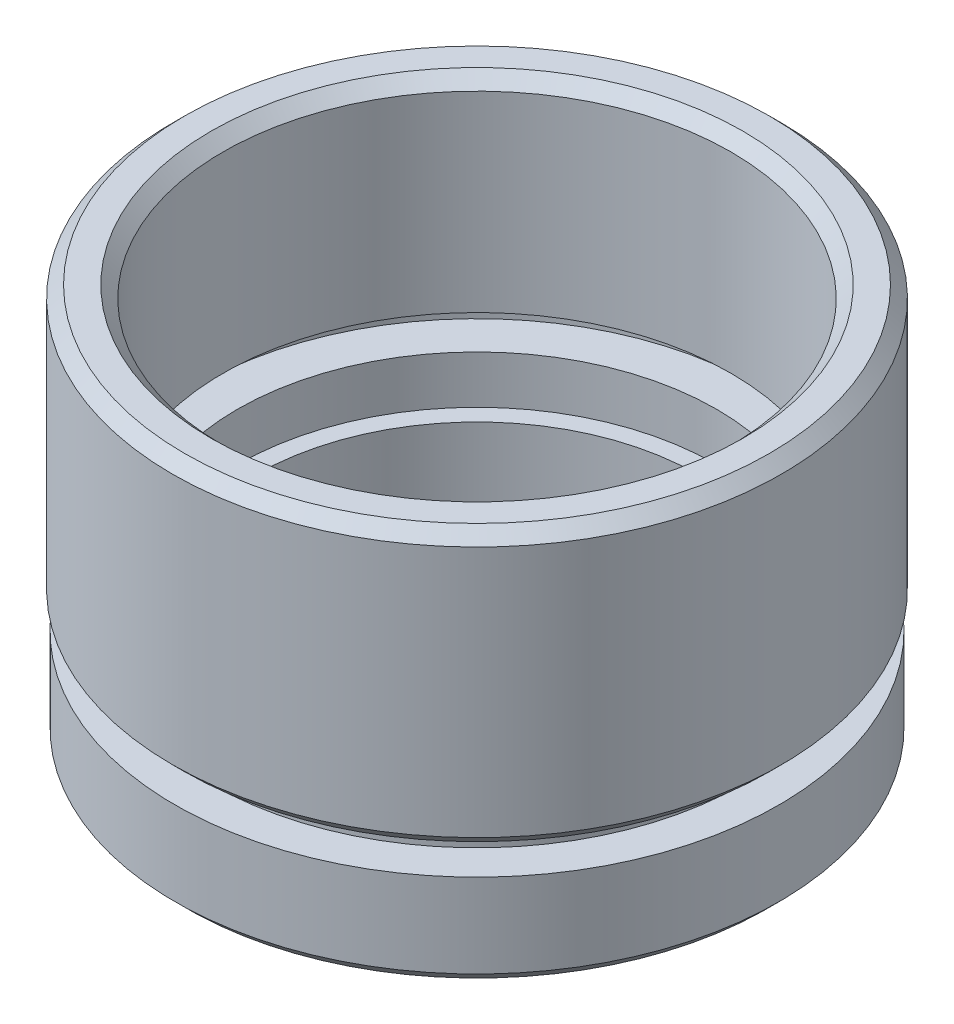
SolidWorks part; units mm, degrees
ref_plane "前视基准面" through (0, 0, 0) normal (0, 0, 1) x (1, 0, 0)
ref_plane "上视基准面" through (0, 0, 0) normal (0, 1, 0) x (1, 0, 0)
ref_plane "右视基准面" through (0, 0, 0) normal (1, 0, 0) x (0, 0, -1)
sketch "草图1" plane through (0, 0, 0) normal (0, 0, 1) x (1, 0, 0)
  line L0 (0, 0) -> (0, 21.8535) construction
  line L1 (9.25, 0) -> (12.6, 0)
  line L2 (12.6, 0) -> (12.6, 4)
  line L3 (12.6, 4) -> (11.1, 4)
  line L4 (11.1, 4) -> (11.1, 5)
  line L5 (11.1, 5) -> (12.7, 5)
  line L6 (12.7, 5) -> (12.7, 16.5)
  line L7 (12.7, 16.5) -> (10.6, 16.5)
  line L8 (10.6, 16.5) -> (10.6, 8)
  line L9 (10.6, 8) -> (11.7, 8)
  line L10 (11.7, 8) -> (11.7, 7)
  line L11 (11.7, 7) -> (10, 7)
  line L12 (10, 7) -> (10, 5)
  line L13 (10, 5) -> (9.25, 5)
  line L14 (9.25, 0) -> (9.25, 5)
  dimension "D1" = 16.5
  dimension "D2" = 12.7
  dimension "D3" = 10.6
  dimension "D4" = 10
  dimension "D5" = 1
  dimension "D6" = 2
  dimension "D7" = 9.25
  dimension "D8" = 12.6
  dimension "D9" = 1
  dimension "D10" = 5
  dimension "D11" = 5
  dimension "D12" = 11.7
  dimension "D13" = 11.1
revolve "旋转1" add sketch "草图1" angle 360 about L0
cosmetic thread "装饰螺纹线11" parameters "D2"=23.2
cosmetic thread "装饰螺纹线12" parameters "D2"=23.2
chamfer "倒角1" distance 0.5 angle 45 4 edges at (0, 16.5, -10.6) (0, 16.5, -12.7) (0, 5, -12.7) (0, 0, -12.6)
